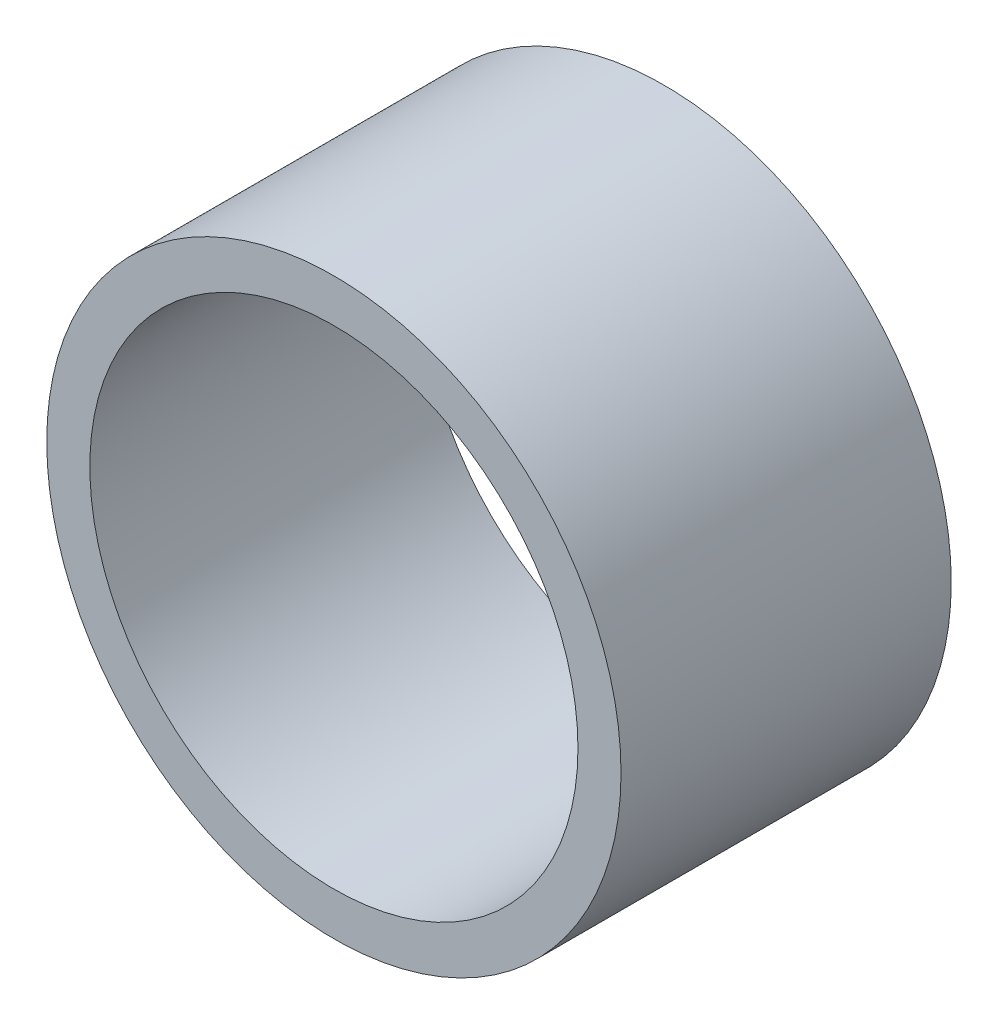
SolidWorks part; units mm, degrees
ref_plane "Front Plane" through (0, 0, 0) normal (0, 0, 1) x (1, 0, 0)
ref_plane "Top Plane" through (0, 0, 0) normal (0, 1, 0) x (1, 0, 0)
ref_plane "Right Plane" through (0, 0, 0) normal (1, 0, 0) x (0, 0, -1)
sketch "Sketch1" plane through (0, 0, 0) normal (0, 0, 1) x (1, 0, 0)
  circle A0 centre (0, 0) radius 15
  circle A1 centre (0, 0) radius 12.75
extrude "Boss-Extrude1" add sketch "Sketch1" along normal blind 17
sketch "Sketch2" plane through (0, 0, 0) normal (0, 0, 1) x (1, 0, 0)
  line L0 (0, 15) -> (0, -15) construction
  line L1 (-15, 0) -> (15, 0) construction
  line L2 (-0.5, 3.2524) -> (-0.5, -3.2008) construction
  line L3 (-4.061, 0.5) -> (3.3195, 0.5) construction
  line L4 (-1, 2.0477) -> (-1, -3.3588) construction
  line L5 (0.5, 3.2524) -> (0.5, -3.2008) construction
  line L6 (-3.5318, 1) -> (1.9113, 1) construction
  line L7 (1, 2.0477) -> (1, -3.3588) construction
  line L8 (-3.5318, -1) -> (1.9113, -1) construction
  line L9 (-4.061, -0.5) -> (3.3195, -0.5) construction
  line L10 (-0.5, 4.9749) -> (-0.5, 8.8609)
  line L11 (-0.5, 8.8609) -> (-1, 8.8609)
  line L12 (-1, 8.8609) -> (-1, 7.3069)
  line L13 (1, 7.3069) -> (1, 8.8609)
  line L14 (1, 8.8609) -> (0.5, 8.8609)
  line L15 (0.5, 8.8609) -> (0.5, 4.9749)
  line L16 (-12.7402, 0.5) -> (-8.8609, 0.5)
  line L17 (-8.8609, 0.5) -> (-8.8609, 1)
  line L18 (-8.8609, 1) -> (-10.3267, 1)
  line L19 (-12.7402, -0.5) -> (-8.8609, -0.5)
  line L20 (-8.8609, -0.5) -> (-8.8609, -1)
  line L21 (-8.8609, -1) -> (-10.3267, -1)
  line L22 (-0.5, -4.9749) -> (-0.5, -8.8609)
  line L23 (-0.5, -8.8609) -> (-1, -8.8609)
  line L24 (-1, -8.8609) -> (-1, -7.3069)
  line L25 (0.5, -4.9749) -> (0.5, -8.8609)
  line L26 (0.5, -8.8609) -> (1, -8.8609)
  line L27 (1, -8.8609) -> (1, -7.3069)
  line L28 (12.7402, 0.5) -> (8.8609, 0.5)
  line L29 (8.8609, 0.5) -> (8.8609, 1)
  line L30 (8.8609, 1) -> (10.3267, 1)
  line L31 (12.7402, -0.5) -> (8.8609, -0.5)
  line L32 (8.8609, -0.5) -> (8.8609, -1)
  line L33 (8.8609, -1) -> (10.3267, -1)
  circle A1 centre (0, 0) radius 15
  arc A2 (-0.5, 4.9749) -> (-0.5, -4.9749) centre (0, 0) ccw
  arc A3 (0.5, 4.9749) -> (0.5, -4.9749) centre (0, 0) cw
  arc A4 (10.3267, 1) -> (-10.3267, 1) centre (0, 0) ccw
  arc A5 (10.3267, -1) -> (-10.3267, -1) centre (0, 0) cw
  circle A6 centre (0, 0) radius 8.875 construction
  arc A7 (-1, 7.3069) -> (-1, -7.3069) centre (0, 0) ccw
  arc A8 (1, 7.3069) -> (1, -7.3069) centre (0, 0) cw
  arc A9 (-12.7402, 0.5) -> (12.7402, 0.5) centre (0, 0) cw
  arc A10 (-12.7402, -0.5) -> (12.7402, -0.5) centre (0, 0) ccw
  dimension "D1" = 0.5
  dimension "D2" = 0.5
  dimension "D3" = 0.5
  dimension "D4" = 0.5
extrude "Boss-Extrude2" add sketch "Sketch2" against normal blind 0.25
